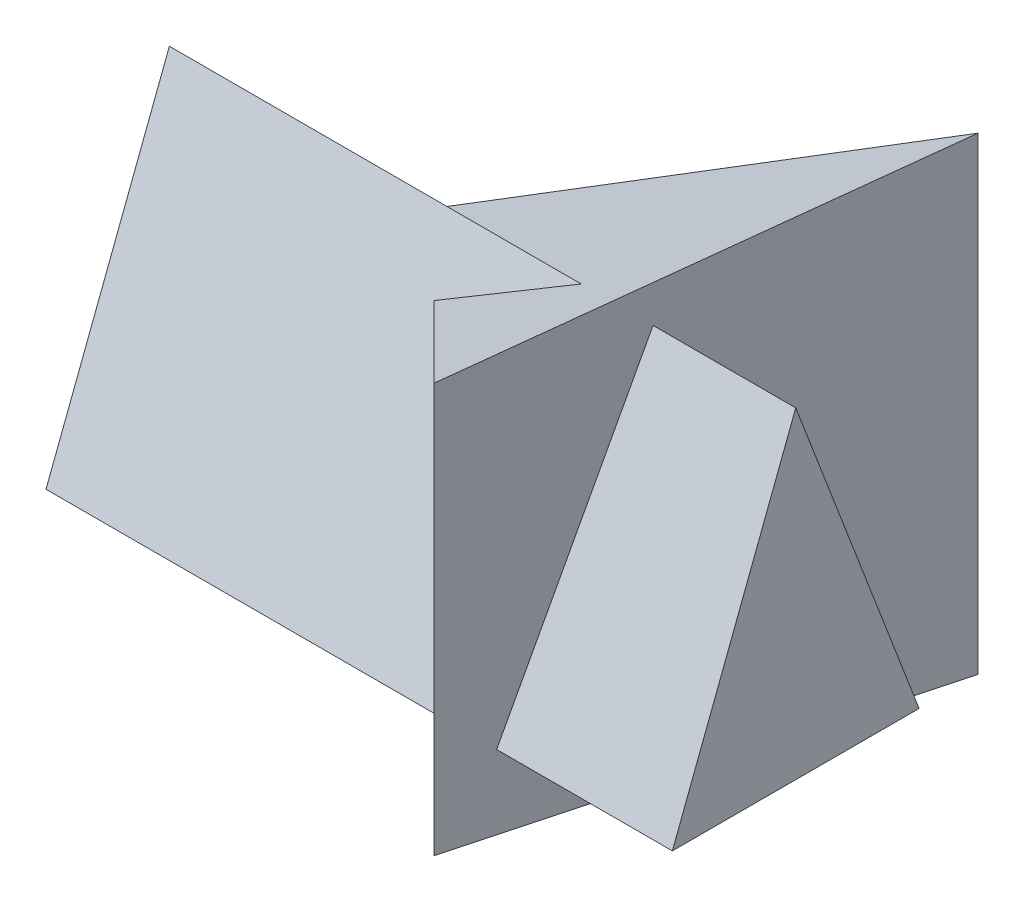
SolidWorks part; units mm, degrees
ref_plane "Front" through (0, 0, 0) normal (0, 0, 1) x (1, 0, 0)
ref_plane "Top" through (0, 0, 0) normal (0, 1, 0) x (1, 0, 0)
ref_plane "Right" through (0, 0, 0) normal (1, 0, 0) x (0, 0, -1)
sketch "Sketch1" plane through (0, 0, 0) normal (0, 1, 0) x (1, 0, 0)
  line L0 (0, 0) -> (44.401, 0) construction
  line L1 (0, 0) -> (86.9333, 23.2937)
  line L2 (86.9333, 23.2937) -> (63.6396, -63.6396)
  line L3 (63.6396, -63.6396) -> (0, 0)
  dimension "D1" = 45
  dimension "D2" = 90
extrude "Extrude1" add sketch "Sketch1" along normal blind 95
sketch "Sketch2" plane through (0, 0, 0) normal (0, 0, 1) x (1, 0, 0)
  line L0 (86.9333, 95) -> (0, 50)
  line L1 (0, 95) -> (0, 0) construction
  line L2 (0, 50) -> (0, 95)
  line L3 (0, 95) -> (86.9333, 95)
  dimension "D1" = 50
extrude "Cut-Extrude1" cut sketch "Sketch2" against normal mid plane 135
sketch "Sketch3" plane through (0, 0, 0) normal (1, 0, 0) x (0, 0, -1)
  line L0 (-28.6396, 80.2571) -> (-3.6396, 15)
  line L1 (-3.6396, 15) -> (-53.6396, 15)
  line L2 (-53.6396, 15) -> (-28.6396, 80.2571)
  line L4 (-63.6396, 82.9423) -> (-63.6396, 0) construction
  line L6 (-63.6396, 0) -> (23.2937, 0) construction
  dimension "D2" = 50
  dimension "D3" = 10
  dimension "D4" = 15
extrude "Extrude2" add sketch "Sketch3" along normal blind 101.93 and the other way blind 25 separate body
